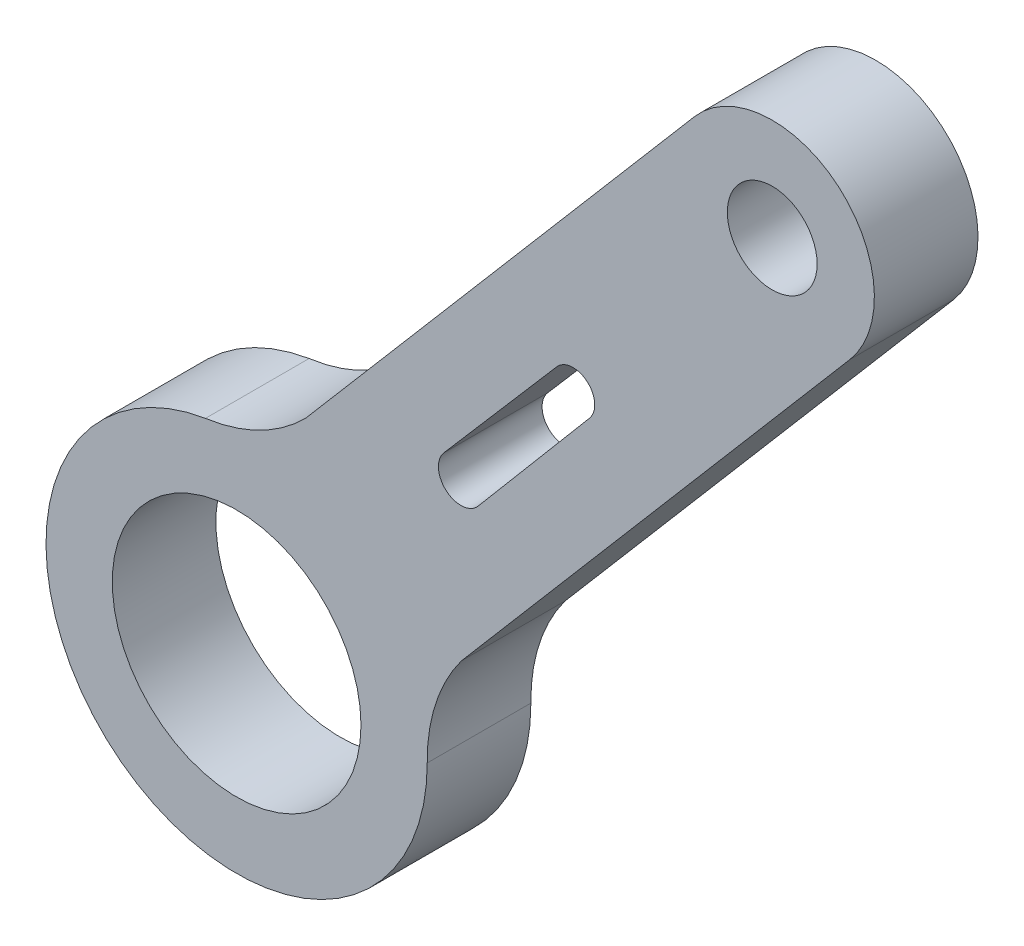
SolidWorks part; units mm, degrees
ref_plane "Front Plane" through (0, 0, 0) normal (0, 0, 1) x (1, 0, 0)
ref_plane "Top Plane" through (0, 0, 0) normal (0, 1, 0) x (1, 0, 0)
ref_plane "Right Plane" through (0, 0, 0) normal (1, 0, 0) x (0, 0, -1)
sketch "Model" plane through (0, 0, 0) normal (0, 0, 1) x (1, 0, 0)
  line L0 (58.0684, 48.5339) -> (46.8301, 35.3658)
  line L1 (47.3143, 39.4872) -> (50.5441, 43.3105)
  line L2 (49.5899, 44.1172) -> (46.3215, 40.3264)
  line L3 (42.3417, 39.2174) -> (53.58, 52.3854)
  line L4 (40.3259, 32.3001) -> (55.8294, 50.4657) construction
  line L5 (53.58, 52.3854) -> (58.0788, 48.546) construction
  line L7 (58.0684, 48.5339) -> (58.0788, 48.546)
  circle A0 centre (40.3259, 32.3001) radius 3.6
  circle A1 centre (55.8294, 50.4657) radius 1.3
  arc A2 (39.4242, 37.7438) -> (42.3417, 39.2174) centre (38.7526, 42.6984) ccw
  arc A3 (39.4242, 37.7438) -> (45.8437, 32.3149) centre (40.3259, 32.3001) ccw
  arc A4 (46.8301, 35.3658) -> (45.8437, 32.3149) centre (50.8431, 32.3835) ccw
  arc A5 (53.58, 52.3854) -> (58.0788, 48.546) centre (55.8294, 50.4657) cw
  arc A6 (50.5441, 43.3105) -> (49.5899, 44.1172) centre (50.067, 43.7138) ccw
  arc A7 (46.3215, 40.3264) -> (47.3143, 39.4872) centre (46.8179, 39.9068) ccw
  point P7 (57.7648, 48.1781)
  point P13 (0, 0)
extrude "Boss-Extrude1" add sketch "Model" along normal blind 3
